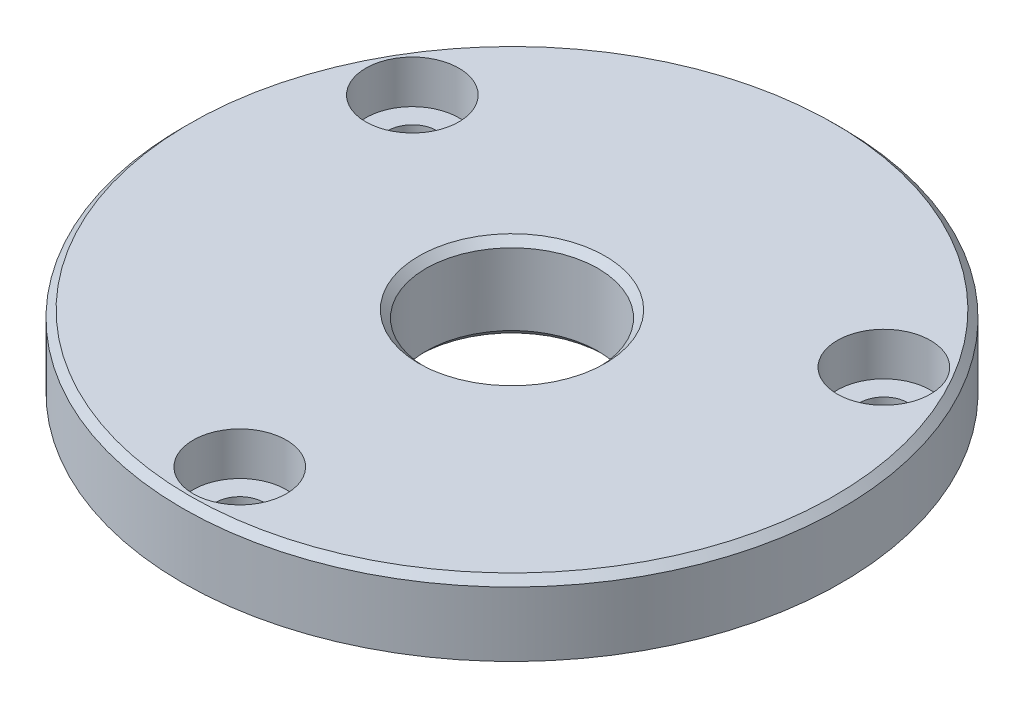
SolidWorks part; units mm, degrees
material "3.1325 (EN-AW 2017A)"
ref_plane "Plan de face" through (0, 0, 0) normal (0, 0, 1) x (1, 0, 0)
ref_plane "Plan de dessus" through (0, 0, 0) normal (0, 1, 0) x (1, 0, 0)
ref_plane "Plan de droite" through (0, 0, 0) normal (1, 0, 0) x (0, 0, -1)
sketch "Esquisse1" plane through (0, 0, 0) normal (0, 0, 1) x (1, 0, 0)
  line L0 (11.75, 0) -> (15, 0)
  line L1 (15, 0) -> (15, 3)
  line L2 (15, 3) -> (23, 3)
  line L3 (23, 3) -> (23, 8)
  line L4 (23, 8) -> (6, 8)
  line L5 (0, 0) -> (0, 12.7798) construction
  line L6 (11.75, 0) -> (11.75, 2)
  line L7 (11.75, 2) -> (6, 2)
  line L8 (6, 2) -> (6, 8)
  dimension "D3" = 3
  dimension "D4" = 5
  dimension "D6" = 2
revolve "Révolution1" add sketch "Esquisse1" angle 360 about L5
chamfer "Chanfrein2" distance 0.5 angle 30 1 edges at (0, 0, -15)
chamfer "Chanfrein3" distance 0.5 angle 45 1 edges at (0, 8, -6)
chamfer "Chanfrein4" distance 0.5 angle 45 1 edges at (0, 2, -6)
chamfer "Chanfrein5" distance 0.5 angle 45 1 edges at (0, 8, -23)
hole_wizard "Chambrage pour vis à tête hexagonale M31" positions "Esquisse4" profile "Esquisse3" counterbore size "M3" standard "ISO" end condition through all
sketch "Esquisse4" plane through (0, 8, 0) normal (0, 1, 0) x (-1, 0, 0)
  point P0 (0, 19)
sketch "Esquisse3" plane through (0, 8, 19) normal (1, 0, 0) x (0, 0, 1)
  line L0 (0, 0) -> (0, 8)
  line L1 (0, 8) -> (1.7, 8)
  line L3 (1.7, 8) -> (1.7, 3)
  line L4 (1.7, 3) -> (3.25, 3)
  line L5 (3.25, 3) -> (3.25, 0)
  line L7 (3.25, 0) -> (0, 0)
  line L11 (0, -6.35) -> (0, 107.95) construction
  dimension "Diamètre du perçage jusqu'au prochain" = 3.4
  dimension "Profondeur du perçage jusqu'au prochain" = 8
  dimension "Diamètre du chambrage" = 6.5
  dimension "Profondeur du chambrage" = 3
pattern_circular "Répétition circulaire1" count 3 over 360 about axis through (0, 0, 0) along (0, 1, 0) of "Chambrage pour vis à tête hexagonale M31"
